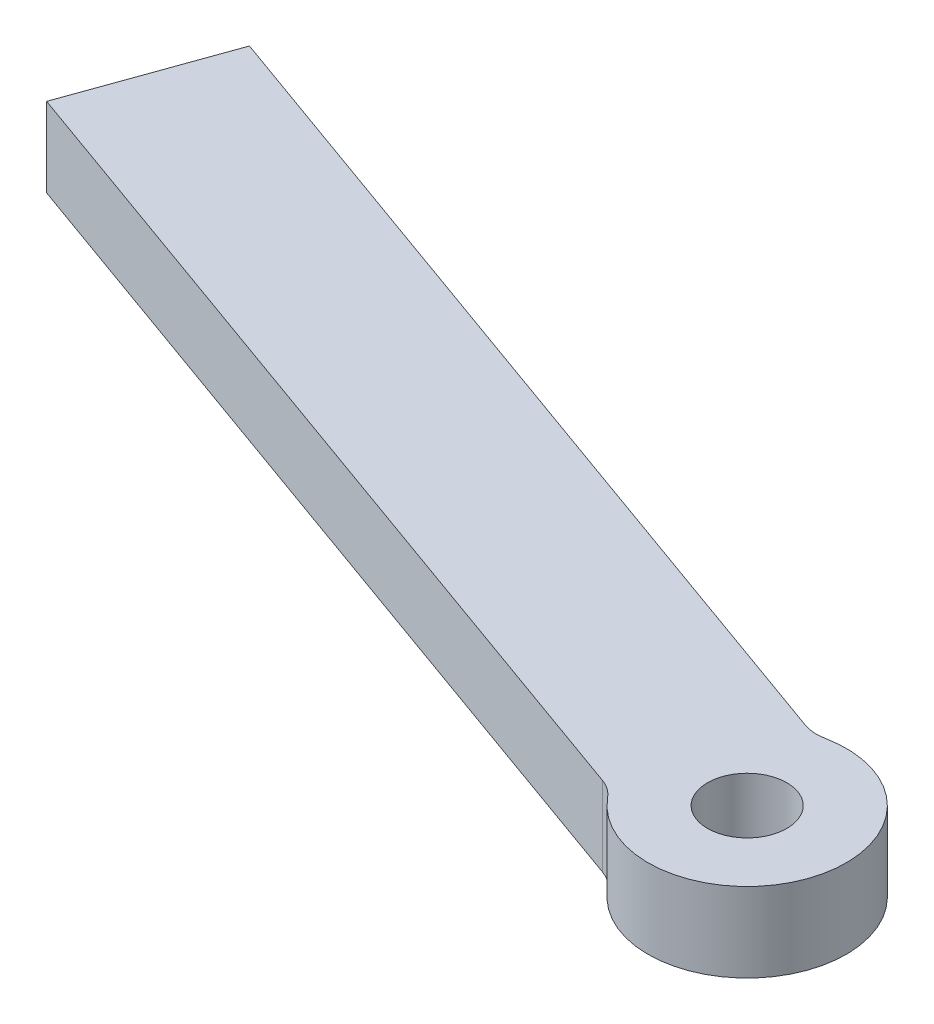
SolidWorks part; units mm, degrees
ref_plane "Front Plane" through (0, 0, 0) normal (0, 0, 1) x (1, 0, 0)
ref_plane "Top Plane" through (0, 0, 0) normal (0, 1, 0) x (1, 0, 0)
ref_plane "Right Plane" through (0, 0, 0) normal (1, 0, 0) x (0, 0, -1)
sketch "Sketch1" plane through (0, 0, 0) normal (0, 1, 0) x (1, 0, 0)
  line L0 (0, 0) -> (-283.949, 101.6936) construction
  line L1 (0, 0) -> (-23.5361, 8.4292) construction
  line L2 (-1.0229, 2.4907) -> (-22.8618, 10.3121)
  line L3 (-2.3716, -1.275) -> (-24.2104, 6.5463)
  line L4 (-22.8618, 10.3121) -> (-24.2104, 6.5463)
  line L5 (0.6743, 1.8829) -> (-22.8618, 10.3121) construction
  line L6 (-0.6743, -1.8829) -> (-24.2104, 6.5463) construction
  line L12 (-213.7381, 76.5482) -> (-283.2244, 103.5577)
  circle A0 centre (0, 0) radius 1
  arc A1 (-1.9348, -1.5832) -> (-0.4898, 2.4516) centre (0, 0) ccw
  arc A2 (-1.0229, 2.4907) -> (-0.4898, 2.4516) centre (-0.6857, 3.4322) ccw
  arc A3 (-2.3716, -1.275) -> (-1.9348, -1.5832) centre (-2.7087, -2.2165) cw
  dimension "D1" = 2
  dimension "D3" = 1
  dimension "D4" = 1
  dimension "D2" = 2
  dimension "D5" = 301.61
extrude "Boss-Extrude1" add sketch "Sketch1" along normal blind 2
